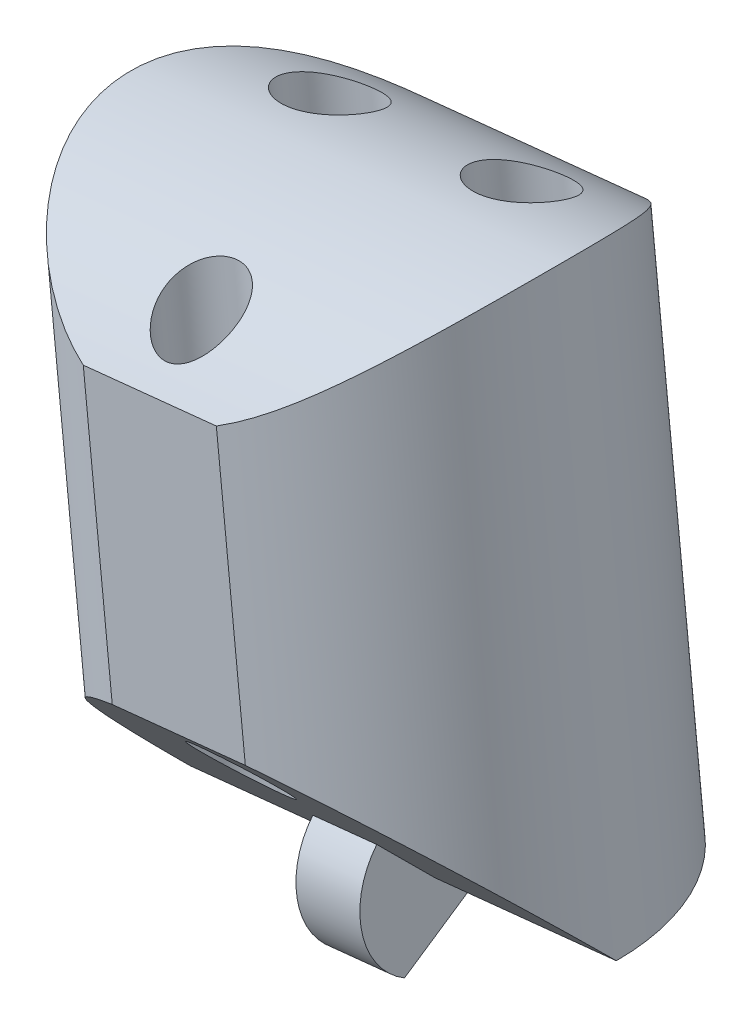
SolidWorks part; units mm, degrees
ref_plane "Front Plane" through (0, 0, 0) normal (0, 0, 1) x (1, 0, 0)
ref_plane "Top Plane" through (0, 0, 0) normal (0, 1, 0) x (1, 0, 0)
ref_plane "Right Plane" through (0, 0, 0) normal (1, 0, 0) x (0, 0, -1)
sketch "Sketch2" plane through (0, 0, 0) normal (0, 0, 1) x (1, 0, 0)
  line L0 (0, 0) -> (90, 0)
  line L1 (90, 0) -> (90, 120)
  line L2 (90, 120) -> (0, 120)
  line L3 (0, 120) -> (0, 0)
  line L4 (0, 120) -> (-10, 120)
  line L5 (-10, 120) -> (-10, 16.9491)
  line L6 (-10, 120) -> (57.5, 127)
  line L7 (57.5, 127) -> (90, 124)
  line L8 (90, 120) -> (99, 60)
  line L10 (90, 124) -> (90, 120)
  line L11 (5.9147, 0) -> (5.9147, -25)
  line L12 (5.9147, -25) -> (-4.0853, -25)
  line L13 (-4.0853, -29) -> (-4.0853, 0)
  line L14 (80, 0) -> (80, -25)
  line L15 (80, -25) -> (90, -25)
  line L16 (90, -29) -> (90, 0)
  line L17 (15.7927, 122.6748) -> (5.4776, 222.1414)
  line L18 (5.4776, 222.1414) -> (21.3923, 223.7918)
  line L19 (21.3923, 223.7918) -> (31.7073, 124.3252)
  line L20 (7.6492, 201.201) -> (23.5639, 202.8514)
  line L21 (10.9066, 169.7905) -> (26.8212, 171.441)
  line L22 (-10, 120) -> (-20.0396, 216.8108)
  line L23 (-20.0396, 216.8108) -> (-4.125, 218.4612)
  line L24 (-4.125, 218.4612) -> (5.9147, 121.6504)
  line L25 (-17.926, 196.4296) -> (-2.0114, 198.08)
  line L26 (-14.7556, 165.8578) -> (1.159, 167.5082)
  line L27 (57.5, 127) -> (46.9095, 229.1223)
  line L28 (46.9095, 229.1223) -> (30.9949, 227.4719)
  line L29 (30.9949, 227.4719) -> (41.5853, 125.3496)
  line L30 (33.2245, 205.9725) -> (49.1391, 207.6229)
  line L31 (36.5688, 173.7233) -> (52.4835, 175.3737)
  line L34 (90, 124) -> (99.1917, 223.5767)
  line L35 (99.1917, 223.5767) -> (83.2594, 225.0473)
  line L36 (83.2594, 225.0473) -> (74.0677, 125.4707)
  line L38 (81.3243, 204.0838) -> (97.2566, 202.6132)
  line L39 (78.4217, 172.6386) -> (94.354, 171.1679)
  line L40 (62.4078, 79.6749) -> (57.5, 127) construction
  line L41 (41.5853, 125.3496) -> (46.4931, 78.0244) construction
  line L42 (46.4931, 78.0244) -> (62.4078, 79.6749) construction
  line L43 (31.7073, 124.3252) -> (36.6151, 77.0001) construction
  line L44 (36.6151, 77.0001) -> (20.7005, 75.3496) construction
  line L45 (20.7005, 75.3496) -> (15.7927, 122.6748) construction
  line L46 (5.9147, 121.6504) -> (10.8224, 74.3253) construction
  line L47 (10.8224, 74.3253) -> (-5.0922, 72.6749) construction
  line L48 (-5.0922, 72.6749) -> (-10, 120) construction
  line L49 (74.0677, 125.4707) -> (69.6944, 78.0931) construction
  line L50 (69.6944, 78.0931) -> (85.7624, 78.0931) construction
  line L51 (85.7624, 78.0931) -> (90, 124) construction
  line L52 (-12.0823, 217.636) -> (10.4873, 0) construction
  line L53 (13.4349, 222.9666) -> (36.5574, 0) construction
  line L54 (38.9522, 228.2971) -> (62.6275, 0) construction
  line L55 (91.2256, 224.312) -> (70.5198, 0) construction
  line L59 (99, 60) -> (93.5277, 44.9649)
  line L60 (99, 60) -> (169.4769, 34.3485)
  line L61 (169.4769, 34.3485) -> (164.0046, 19.3134)
  line L62 (164.0046, 19.3134) -> (93.5277, 44.9649)
  line L63 (90, -2) -> (100, -2)
  line L64 (141.2862, 44.6091) -> (135.8138, 29.574)
  line L65 (99, 60) -> (55.7741, 75.7329) construction
  line L66 (55.7741, 75.7329) -> (50.3018, 60.6978) construction
  line L67 (100, -2) -> (100, -29)
  line L70 (-4.0853, -2) -> (-14.0853, -2)
  line L71 (-14.0853, -2) -> (-14.0853, -29)
  line L74 (-4.0853, 0) -> (0, 0)
  line L75 (-14.0853, -29) -> (-14.0853, -112.587)
  line L76 (-14.0853, -112.587) -> (100, -112.587)
  line L77 (100, -112.587) -> (100, -29)
  line L78 (-14.0853, -29) -> (100, -29)
  line L79 (-14.0853, -14.5) -> (100, -14.5) construction
  line L80 (31.7073, -112.587) -> (31.7073, -122.6232)
  line L81 (31.7073, -122.6232) -> (42.9573, -122.6232)
  line L82 (42.9573, -122.6232) -> (42.9573, -112.587)
  line L83 (-14.0853, -112.587) -> (-88.3667, -112.587)
  line L84 (-88.3667, -112.587) -> (-88.3667, -128.2699)
  line L85 (-88.3667, -128.2699) -> (169.4958, -128.2699)
  line L86 (169.4958, -128.2699) -> (169.4958, -112.587)
  line L87 (169.4958, -112.587) -> (100, -112.587)
  line L88 (90, 60) -> (-10, 60) construction
  line L89 (50.3018, 60.6978) -> (93.5277, 44.9649) construction
  line L90 (87.2806, 55.7521) -> (166.7408, 26.8309) construction
  line L91 (87.2806, 55.7521) -> (82.1749, 52.5336) construction
  line L92 (82.1749, 52.5336) -> (77.3257, 0) construction
  line L93 (83.1185, 56.6957) -> (86.337, 51.59) construction
  arc A0 (-10, 16.9491) -> (-4.0853, 0) centre (14.9876, 16.1624) ccw
  arc A1 (93.5277, 44.9649) -> (90, 0) centre (-126.4069, 39.5988) cw
  point P42 (41.1818, 206.7977)
  point P100 (84.7278, 54.1428)
  point P101 (84.7278, 54.1428)
  dimension "D11" = 47.3684
  dimension "D35" = 9
  dimension "D32" = 220
  dimension "D36" = 25
  dimension "D1" = 120
  dimension "D2" = 90
  dimension "D3" = 10
  dimension "D5" = 67.862
  dimension "D6" = 7
  dimension "D7" = 4
  dimension "D8" = 16
  dimension "D9" = 16
  dimension "D10" = 100
  dimension "D12" = 31.5789
  dimension "D13" = 16
  dimension "D14" = 16
  dimension "D15" = 16
  dimension "D16" = 25.7927
  dimension "D17" = 100
  dimension "D18" = 21.0526
  dimension "D19" = 31.5789
  dimension "D20" = 97.33
  dimension "D21" = 102.67
  dimension "D22" = 20.4905
  dimension "D23" = 30.7358
  dimension "D24" = 21.6147
  dimension "D25" = 32.4221
  dimension "D26" = 25
  dimension "D28" = 25
  dimension "D29" = 75
  dimension "D30" = 47.5789
  dimension "D31" = 30
  dimension "D33" = 46
  dimension "D34" = 20
  dimension "D37" = 2
  dimension "D38" = 2
  dimension "D39" = 27
  dimension "D40" = 10
  dimension "D41" = 10
  dimension "D42" = 27
  dimension "D43" = 14.5
  dimension "D44" = 127.5
ref_plane "Plane1" through (87.2806, 55.7521, 0) normal (-0.846, -0.5333, 0) x (0, 0, 1)
ref_plane "Plane2" through (82.1749, 52.5336, 0) normal (-0.0919, -0.9958, 0) x (-0.9958, 0.0919, 0)
ref_plane "Plane3" through (91.2256, 224.312, 0) normal (-0.0919, -0.9958, 0) x (-0.9958, 0.0919, 0)
ref_plane "Plane4" through (38.9522, 228.2971, 0) normal (0.1032, -0.9947, 0) x (-0.9947, -0.1032, 0)
ref_plane "Plane5" through (13.4349, 222.9666, 0) normal (0.1032, -0.9947, 0) x (-0.9947, -0.1032, 0)
ref_plane "Plane7" through (166.7408, 26.8309, 0) normal (0.9397, -0.342, 0) x (0, 0, -1)
ref_plane "Plane8" through (110.4217, -40.1902, 0) normal (0.9397, -0.342, 0) x (0, 0, -1)
ref_plane "Plane9" through (19.3664, 209.803, 0) normal (-0.0919, -0.9958, 0) x (-0.9958, 0.0919, 0)
ref_plane "Plane10" through (16.4638, 178.3578, 0) normal (-0.0919, -0.9958, 0) x (-0.9958, 0.0919, 0)
ref_plane "Plane11" through (-20.7793, 200.3721, 0) normal (0.1032, -0.9947, 0) x (-0.9947, -0.1032, 0)
ref_plane "Plane12" through (-17.435, 168.1229, 0) normal (0.1032, -0.9947, 0) x (-0.9947, -0.1032, 0)
ref_plane "Plane13" through (-20.5619, 198.2754, 0) normal (0.1032, -0.9947, 0) x (-0.9947, -0.1032, 0)
ref_plane "Plane14" through (-17.3045, 166.8649, 0) normal (0.1032, -0.9947, 0) x (-0.9947, -0.1032, 0)
ref_plane "Plane15" through (-12.0823, 217.636, 0) normal (0.1032, -0.9947, 0) x (-0.9947, -0.1032, 0)
ref_plane "Plane16" through (-20.3445, 196.1788, 0) normal (0.1032, -0.9947, 0) x (-0.9947, -0.1032, 0)
ref_plane "Plane17" through (-17.1741, 165.607, 0) normal (0.1032, -0.9947, 0) x (-0.9947, -0.1032, 0)
ref_plane "Plane18" through (12.1098, 131.1899, 0) normal (-0.0919, -0.9958, 0) x (-0.9958, 0.0919, 0)
ref_plane "Plane19" through (-12.4184, 119.7492, 0) normal (0.1032, -0.9947, 0) x (-0.9947, -0.1032, 0)
ref_plane "Plane20" through (0, 0, 0) normal (0, 0, 1) x (0.1032, -0.9947, 0)
ref_plane "Plane21" through (0, 0, 0) normal (0, 0, 1) x (-0.0919, -0.9958, 0)
ref_plane "Plane22" through (10.3758, 1.076, 0) normal (-0.9947, -0.1032, 0) x (0.1032, -0.9947, 0)
ref_plane "Plane23" through (36.1684, 3.7508, 0) normal (-0.9947, -0.1032, 0) x (0.1032, -0.9947, 0)
ref_plane "Plane24" through (61.9611, 6.4256, 0) normal (-0.9947, -0.1032, 0) x (0.1032, -0.9947, 0)
ref_plane "Plane25" through (69.924, -6.4545, 0) normal (-0.9958, 0.0919, 0) x (-0.0919, -0.9958, 0)
sketch "Sketch3" plane through (-12.0823, 217.636, 0) normal (0.1032, -0.9947, 0) x (-0.9947, -0.1032, 0)
  circle A0 centre (0, 0) radius 8
  dimension "D1" = 16
extrude "Boss-Extrude1" add sketch "Sketch3" along normal blind 21.6147
sketch "Sketch4" plane through (10.3758, 1.076, 0) normal (-0.9947, -0.1032, 0) x (0.1032, -0.9947, 0)
  line L0 (-217.7214, 8) -> (-213.7214, 8)
  line L1 (-196.1067, 8) -> (-217.7214, 8) construction
  line L2 (-217.7214, 8) -> (-217.7214, -8)
  line L3 (-217.7214, -8) -> (-213.7214, -8)
  line L4 (-217.7214, -8) -> (-196.1067, -8) construction
  arc A0 (-213.7214, 8) -> (-213.7214, -8) centre (-207.3937, 0) ccw
  dimension "D2" = 10.2
  dimension "D1" = 4
extrude "Cut-Extrude1" cut sketch "Sketch4" against normal through all and the other way through all
sketch "Sketch5" plane through (10.3758, 1.076, 0) normal (-0.9947, -0.1032, 0) x (0.1032, -0.9947, 0)
  line L0 (-196.1067, 0) -> (-204.1067, 8)
  line L1 (-196.1067, -8) -> (-196.1067, 8) construction
  line L2 (-196.1067, 8) -> (-213.7214, 8) construction
  line L3 (-204.1067, 8) -> (-196.1067, 8)
  line L4 (-196.1067, 8) -> (-196.1067, 0)
  dimension "D1" = 45
extrude "Cut-Extrude2" cut sketch "Sketch5" against normal through all and the other way through all
sketch "Sketch7" plane through (10.3758, 1.076, 0) normal (-0.9947, -0.1032, 0) x (0.1032, -0.9947, 0)
  line L11 (-198.0866, 1.9799) -> (-196.1067, 0)
  line L14 (-196.1067, 0) -> (-196.1067, -2.8)
  line L15 (-196.1067, -2.8) -> (-193.6818, 1.4)
  line L16 (-196.1067, 0) -> (-204.1067, 8) construction
  arc A0 (-198.0866, 1.9799) -> (-193.6818, 1.4) centre (-196.1067, 0) cw
  dimension "D2" = 2.8
  dimension "D1" = 30
  dimension "D3" = 2.8
extrude "Boss-Extrude3" add sketch "Sketch7" along normal mid plane 2.4
sketch "Sketch8" plane through (-12.0823, 217.636, 0) normal (0.1032, -0.9947, 0) x (-0.9947, -0.1032, 0)
  line L0 (8, 0) -> (-8, 0) construction
  circle A0 centre (-3.6, 3) radius 1.6
  circle A1 centre (3.6, 3) radius 1.6
  circle A3 centre (0, -5.5) radius 1.4
  point P6 (0, 0)
  dimension "D1" = 3.2
  dimension "D2" = 3.2
  dimension "D7" = 2.8
  dimension "D3" = 3
  dimension "D4" = 3
  dimension "D5" = 3.6
  dimension "D6" = 3.6
  dimension "D8" = 5.5
extrude "Cut-Extrude3" cut sketch "Sketch8" against normal through all and the other way through all
sketch "Sketch9" plane through (-20.2285, 195.0606, 0) normal (0.1032, -0.9947, 0) x (0.9947, 0.1032, 0)
  line L0 (7.9334, -7.6) -> (12.9294, -7.6)
  line L1 (2.4314, 0) -> (18.4314, 0) construction
  line L2 (7.9334, 7.6) -> (12.9294, 7.6)
  arc A0 (2.4314, 0) -> (18.4314, 0) centre (10.4314, 0) ccw construction
  arc A1 (7.9334, -7.6) -> (12.9294, -7.6) centre (10.4314, 0) ccw
  arc A2 (18.4314, 0) -> (2.4314, 0) centre (10.4314, 0) ccw construction
  arc A3 (7.9334, 7.6) -> (12.9294, 7.6) centre (10.4314, 0) cw
  point P14 (10.4314, 7.6)
  dimension "D1" = 7.6
  dimension "D2" = 7.6
extrude "Cut-Extrude4" cut sketch "Sketch9" against normal through all
